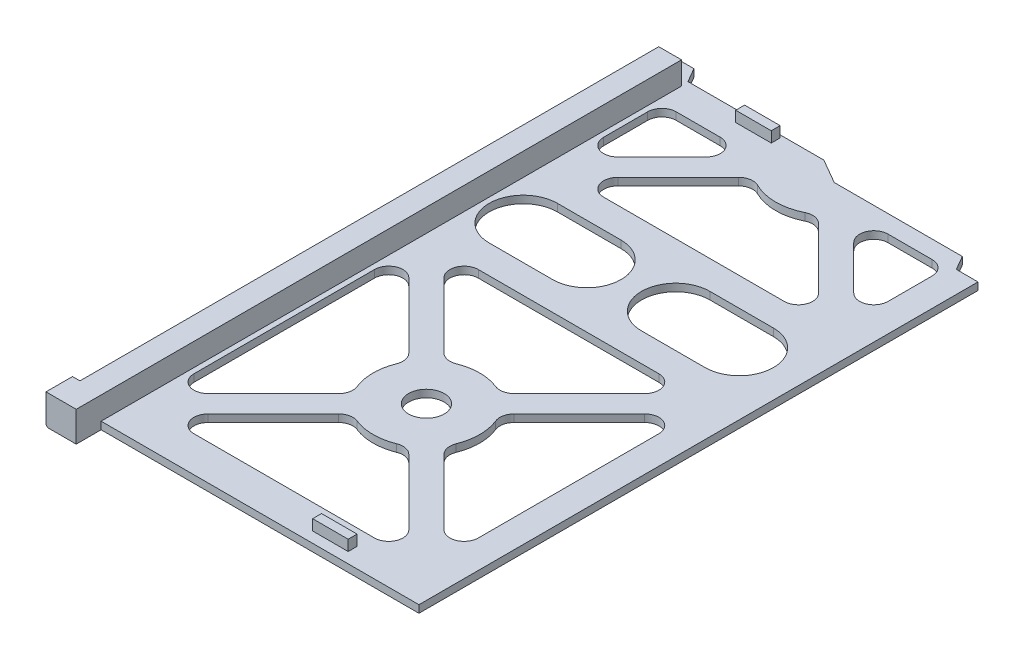
SolidWorks part; units mm, degrees
ref_plane "Front Plane" through (0, 0, 0) normal (0, 0, 1) x (1, 0, 0)
ref_plane "Top Plane" through (0, 0, 0) normal (0, 1, 0) x (1, 0, 0)
ref_plane "Right Plane" through (0, 0, 0) normal (1, 0, 0) x (0, 0, -1)
sketch "Sketch1" plane through (0, 0, 0) normal (0, 1, 0) x (1, 0, 0)
  line L0 (-48.95, -172.25) -> (-48.95, 0.55)
  line L1 (-40.6406, 0) -> (1.05, 0)
  line L2 (48.95, -8) -> (48.95, -165.25)
  line L5 (48.95, -165.25) -> (-40.45, -165.25)
  line L6 (-40.45, -165.25) -> (-40.45, -172.25)
  line L7 (-40.45, -172.25) -> (-48.95, -172.25)
  line L8 (-27.1718, -148.4216) -> (-8.8192, -130.0689)
  line L9 (-34.95, -9) -> (-22.5566, -9)
  line L10 (-38.95, -13) -> (-38.95, -25.3934)
  line L11 (-24.3434, -155.25) -> (26.4434, -155.25)
  line L12 (41.05, -13) -> (41.05, -25.3934)
  line L13 (-32.1216, -143.4718) -> (-13.7689, -125.1192)
  line L14 (29.2718, -148.4216) -> (10.9192, -130.0689)
  line L15 (34.2216, -143.4718) -> (15.8689, -125.1192)
  line L16 (15.8689, -105.3808) -> (34.2216, -87.0282)
  line L17 (-13.7689, -105.3808) -> (-32.1216, -87.0282)
  line L18 (10.9192, -100.4311) -> (29.2718, -82.0784)
  line L19 (-27.1718, -82.0784) -> (-8.8192, -100.4311)
  line L20 (-27.1718, -33.1716) -> (-10.2023, -16.2021)
  line L21 (-32.1216, -28.2218) -> (-19.7282, -15.8284)
  line L22 (29.2718, -33.1716) -> (12.3023, -16.2021)
  line L23 (34.2216, -28.2218) -> (21.8282, -15.8284)
  line L24 (41.05, -89.8566) -> (41.05, -140.6434)
  line L25 (-24.3434, -40) -> (26.4434, -40)
  line L29 (-38.95, -89.8566) -> (-38.95, -140.6434)
  line L34 (24.6566, -9) -> (37.05, -9)
  line L35 (41.05, -155.25) -> (-38.95, -75.25) construction
  line L36 (-38.95, -9) -> (41.05, -9) construction
  line L37 (-38.95, -9) -> (-38.95, -155.25) construction
  line L38 (-38.95, -155.25) -> (41.05, -155.25) construction
  line L39 (41.05, -9) -> (41.05, -155.25) construction
  line L40 (-38.95, -9) -> (41.05, -155.25) construction
  line L41 (-38.95, -155.25) -> (41.05, -9) construction
  line L42 (-38.95, -155.25) -> (41.05, -75.25) construction
  line L43 (1.05, 0) -> (-38.95, -40) construction
  line L44 (1.05, 0) -> (41.05, -40) construction
  line L45 (-24.3434, -75.25) -> (26.4434, -75.25)
  line L46 (-29.325, -57.625) -> (-11.45, -57.625) construction
  line L47 (-29.325, -48) -> (-11.45, -48)
  line L48 (-29.325, -67.25) -> (-11.45, -67.25)
  line L49 (13.55, -57.625) -> (31.425, -57.625) construction
  line L50 (13.55, -48) -> (31.425, -48)
  line L51 (13.55, -67.25) -> (31.425, -67.25)
  line L52 (-2.4141, 0) -> (4.5141, -4)
  line L53 (4.5141, -4) -> (40.5406, -4)
  line L54 (40.5406, -4) -> (42.85, -8)
  line L55 (42.85, -8) -> (48.95, -8)
  line L56 (-48.95, 0.55) -> (-48.95, 4)
  line L57 (-48.95, 4) -> (-42.95, 4)
  line L58 (-42.95, 4) -> (-40.6406, 0)
  circle A0 centre (1.05, -115.25) radius 5
  arc A1 (-4.5085, -129.1821) -> (6.6085, -129.1821) centre (1.05, -115.25) ccw
  arc A2 (-5.6004, -15.4451) -> (7.7004, -15.4451) centre (1.05, -2) ccw
  arc A3 (-12.8821, -109.6915) -> (-12.8821, -120.8085) centre (1.05, -115.25) ccw
  arc A4 (6.6085, -101.3179) -> (-4.5085, -101.3179) centre (1.05, -115.25) ccw
  arc A5 (14.9821, -120.8085) -> (14.9821, -109.6915) centre (1.05, -115.25) ccw
  arc A8 (41.05, -140.6434) -> (34.2216, -143.4718) centre (37.05, -140.6434) cw
  arc A9 (26.4434, -155.25) -> (29.2718, -148.4216) centre (26.4434, -151.25) ccw
  arc A10 (41.05, -89.8566) -> (34.2216, -87.0282) centre (37.05, -89.8566) ccw
  arc A11 (26.4434, -75.25) -> (29.2718, -82.0784) centre (26.4434, -79.25) cw
  arc A12 (-24.3434, -75.25) -> (-27.1718, -82.0784) centre (-24.3434, -79.25) ccw
  arc A13 (-32.1216, -87.0282) -> (-38.95, -89.8566) centre (-34.95, -89.8566) ccw
  arc A14 (15.8689, -125.1192) -> (14.9821, -120.8085) centre (18.6973, -122.2907) cw
  arc A15 (15.8689, -105.3808) -> (14.9821, -109.6915) centre (18.6973, -108.2093) ccw
  arc A16 (10.9192, -100.4311) -> (6.6085, -101.3179) centre (8.0907, -97.6027) cw
  arc A17 (-4.5085, -101.3179) -> (-8.8192, -100.4311) centre (-5.9907, -97.6027) cw
  arc A18 (-12.8821, -109.6915) -> (-13.7689, -105.3808) centre (-16.5973, -108.2093) ccw
  arc A19 (-12.8821, -120.8085) -> (-13.7689, -125.1192) centre (-16.5973, -122.2907) cw
  arc A20 (10.9192, -130.0689) -> (6.6085, -129.1821) centre (8.0907, -132.8973) ccw
  arc A21 (-4.5085, -129.1821) -> (-8.8192, -130.0689) centre (-5.9907, -132.8973) ccw
  arc A22 (-32.1216, -143.4718) -> (-38.95, -140.6434) centre (-34.95, -140.6434) cw
  arc A23 (-24.3434, -155.25) -> (-27.1718, -148.4216) centre (-24.3434, -151.25) cw
  arc A24 (41.05, -13) -> (37.05, -9) centre (37.05, -13) ccw
  arc A25 (-34.95, -9) -> (-38.95, -13) centre (-34.95, -13) ccw
  arc A26 (-32.1216, -28.2218) -> (-38.95, -25.3934) centre (-34.95, -25.3934) cw
  arc A27 (-22.5566, -9) -> (-19.7282, -15.8284) centre (-22.5566, -13) cw
  arc A28 (24.6566, -9) -> (21.8282, -15.8284) centre (24.6566, -13) ccw
  arc A29 (41.05, -25.3934) -> (34.2216, -28.2218) centre (37.05, -25.3934) cw
  arc A30 (29.2718, -33.1716) -> (26.4434, -40) centre (26.4434, -36) cw
  arc A31 (-24.3434, -40) -> (-27.1718, -33.1716) centre (-24.3434, -36) cw
  arc A32 (12.3023, -16.2021) -> (7.7004, -15.4451) centre (9.4739, -19.0305) ccw
  arc A33 (-5.6004, -15.4451) -> (-10.2023, -16.2021) centre (-7.3739, -19.0305) ccw
  arc A34 (-29.325, -48) -> (-29.325, -67.25) centre (-29.325, -57.625) ccw
  arc A35 (-11.45, -67.25) -> (-11.45, -48) centre (-11.45, -57.625) ccw
  arc A36 (13.55, -48) -> (13.55, -67.25) centre (13.55, -57.625) ccw
  arc A37 (31.425, -67.25) -> (31.425, -48) centre (31.425, -57.625) ccw
  point P4 (-40.45, -168.75)
  point P28 (-20.3875, -57.625)
  point P45 (1.05, -82.125)
  point P49 (1.05, -115.25)
  point P60 (41.05, -80.1997)
  point P67 (-38.95, -80.1997)
  point P70 (13.8387, -123.089)
  point P75 (8.889, -102.4613)
  point P80 (-11.7387, -107.411)
  point P112 (22.4875, -57.625)
  dimension "D20" = 10
  dimension "D22" = 4
  dimension "D23" = 4
  dimension "D24" = 4
  dimension "D25" = 4
  dimension "D1" = 8.5
  dimension "D2" = 97.9
  dimension "D3" = 48.95
  dimension "D4" = 7
  dimension "D7" = 10
  dimension "D8" = 7.9
  dimension "D9" = 10
  dimension "D11" = 7
  dimension "D12" = 7
  dimension "D6" = 45
  dimension "D13" = 45
  dimension "D14" = 80
  dimension "D15" = 40
  dimension "D16" = 7
  dimension "D17" = 7
  dimension "D18" = 45
  dimension "D19" = 45
  dimension "D10" = 9
  dimension "D21" = 10
  dimension "D26" = 8
  dimension "D27" = 8
  dimension "D28" = 25
  dimension "D29" = 40
  dimension "D30" = 30
  dimension "D31" = 4
  dimension "D32" = 60
  dimension "D33" = 6.1
  dimension "D34" = 4
  dimension "D35" = 6
  dimension "D36" = 60
  dimension "D37" = 4
  dimension "D5" = 170.25
extrude "Boss-Extrude1" add sketch "Sketch1" along normal blind 2.1 contours L58 L57 L56 L0 L7 L6 L5 L2 L55 L54 L53 L52 L1 A37 L51 A36 L50 A35 L48 A34 L47 A33 A2 A32 L22 A30 L25 A31 L20 A15 L16 A10 L24 A8 L15 A14 A5 A0 A4 A17 L19 A12 L45 A11 L18 | L29 A22 L13 A19 A3 A18 L17 A13 | L21 A27 L9 A25 L10 A26 | A1 A20 L14 A9 L11 A23 L8 A21 | L23 A28 L34 A24 L12 A29
sketch "Sketch2" plane through (0, 2.1, 0) normal (0, 1, 0) x (1, 0, 0)
  line L0 (-40.45, -165.25) -> (-40.45, -172.25) construction
  line L1 (-48.95, -172.25) -> (-40.45, -172.25)
  line L2 (-48.95, -172.25) -> (-48.95, -2)
  line L3 (-48.95, -2) -> (-40.45, -2)
  line L4 (-40.45, -172.25) -> (-40.45, -2)
  line L5 (-48.95, -172.25) -> (-40.45, -2) construction
  line L6 (-48.95, -2) -> (-40.45, -172.25) construction
  line L7 (-48.95, -2) -> (1.05, -2) construction
  line L8 (-2.4141, 0) -> (4.5141, -4) construction
  point P4 (-44.7, -87.125)
extrude "Boss-Extrude2" add sketch "Sketch2" along normal blind 6.4
sketch "Sketch3" plane through (-48.95, 0, 0) normal (-1, 0, 0) x (0, 0, 1)
  line L0 (165.25, 2.1) -> (165.25, 0) construction
  line L1 (165.25, 2.1) -> (165.25, 0)
  line L3 (164.8, 2.1) -> (2, 2.1)
  line L4 (164.8, 2.1) -> (164.8, 8.5)
  line L5 (164.8, 8.5) -> (2, 8.5)
  line L6 (2, 2.1) -> (2, 8.5)
  line L7 (164.8, 2.1) -> (2, 8.5) construction
  line L8 (164.8, 8.5) -> (2, 2.1) construction
  line L9 (2, 2.1) -> (-4, 2.1) construction
  point P6 (83.4, 5.3)
  line M7 (172.25, 8.5) -> (2, 8.5)
  line M8 (2, 8.5) -> (2, 2.1)
extrude "Cut-Extrude1" cut sketch "Sketch3" against normal blind 2.1 contours L6 L3 L1 L4 M7 M8
sketch "Sketch4" plane through (0, 2.1, 0) normal (0, 1, 0) x (1, 0, 0)
  line L0 (1.05, -2) -> (-40.45, -2) construction
  line L1 (-2.4141, 0) -> (4.5141, -4) construction
  line L2 (1.05, -2) -> (1.05, -173.0382) construction
  line L3 (-23.95, -0.75) -> (-13.95, -0.75)
  line L4 (-23.95, -0.75) -> (-23.95, -3.25)
  line L5 (-23.95, -3.25) -> (-13.95, -3.25)
  line L6 (-13.95, -0.75) -> (-13.95, -3.25)
  line L7 (-23.95, -0.75) -> (-13.95, -3.25) construction
  line L8 (-23.95, -3.25) -> (-13.95, -0.75) construction
  line L9 (16.05, -159.75) -> (26.05, -159.75)
  line L10 (16.05, -159.75) -> (16.05, -162.25)
  line L11 (16.05, -162.25) -> (26.05, -162.25)
  line L12 (26.05, -159.75) -> (26.05, -162.25)
  line L13 (16.05, -159.75) -> (26.05, -162.25) construction
  line L14 (16.05, -162.25) -> (26.05, -159.75) construction
  line L15 (48.95, -165.25) -> (-40.45, -165.25) construction
  point P9 (-18.95, -2)
  point P14 (21.05, -161)
  dimension "D1" = 2.5
  dimension "D2" = 10
  dimension "D3" = 15
  dimension "D4" = 15
  dimension "D5" = 3
extrude "Boss-Extrude3" add sketch "Sketch4" along normal blind 3
chamfer "Chamfer1" distance 0.5 angle 45 1 edges at (-48.95, 0, 84.125)
equation "\"D3@Sketch1\"=\"D2@Sketch1\"/2"
equation "\"D12@Sketch1\"=\"D11@Sketch1\""
equation "\"D16@Sketch1\"=\"D11@Sketch1\""
equation "\"D17@Sketch1\"=\"D11@Sketch1\""
equation "\"D19@Sketch1\"=\"D18@Sketch1\""
equation "\"D13@Sketch1\"=\"D6@Sketch1\""
equation "\"D15@Sketch1\"=\"D14@Sketch1\"/2"
equation "\"D22@Sketch1\"=\"D23@Sketch1\""
equation "\"D27@Sketch1\"=\"D26@Sketch1\""
equation "\"D29@Sketch1\"=\"D15@Sketch1\""
equation "\"D37@Sketch1\"=\"D34@Sketch1\""
equation "\"D1@Boss-Extrude2\"=8.5-2.1"
equation "\"D4@Sketch4\"=\"D3@Sketch4\""
